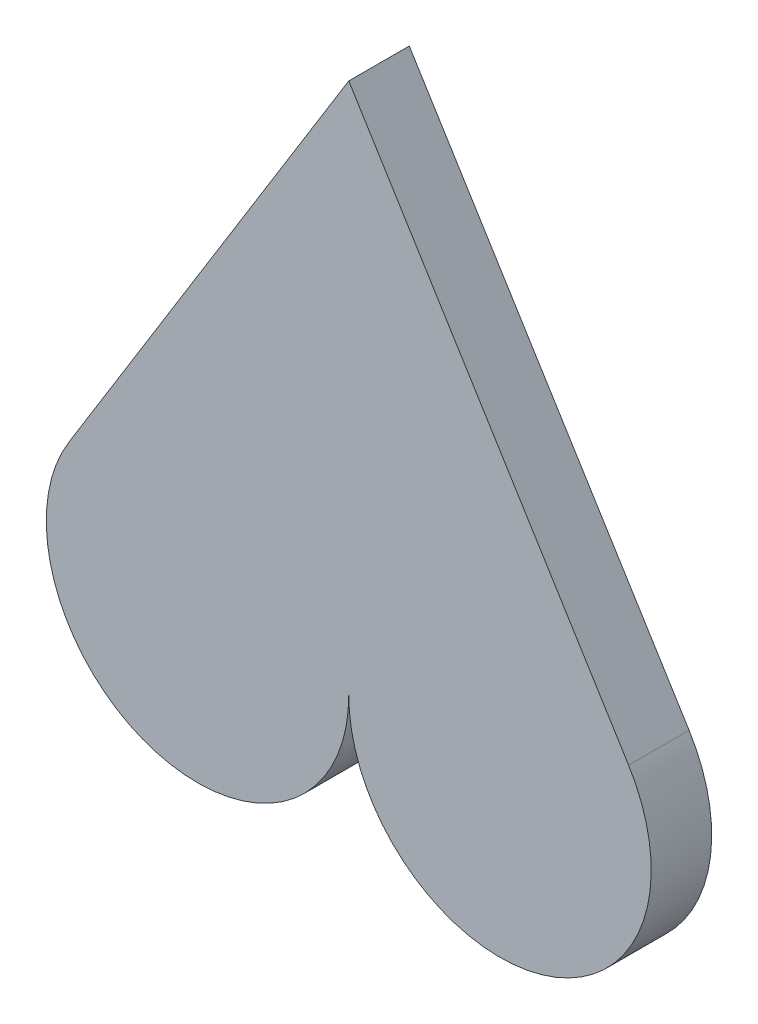
SolidWorks part; units mm, degrees
ref_plane "Front Plane" through (0, 0, 0) normal (0, 0, 1) x (1, 0, 0)
ref_plane "Top Plane" through (0, 0, 0) normal (0, 1, 0) x (1, 0, 0)
ref_plane "Right Plane" through (0, 0, 0) normal (1, 0, 0) x (0, 0, -1)
sketch "Sketch1" plane through (0, 0, 0) normal (0, 0, -1) x (1, 0, 0)
  line L0 (0, 0) -> (-27.7593, 44.9025)
  line L1 (-1000, 0) -> (49000, 0) construction
  line L8 (-0.0012, 0) -> (27.7581, 44.9025)
  arc A0 (-0.0006, 52.7901) -> (-27.7593, 44.9025) centre (-15.0006, 52.7901) ccw
  arc A4 (-0.0006, 52.7901) -> (27.7581, 44.9025) centre (14.9994, 52.7901) cw
  point P2 (-15.0006, 52.7901)
  point P9 (-5.0006, 52.7901)
  point P10 (-23.5064, 47.5317)
  point P11 (4.2529, 2.6292)
  dimension "D1" = 52.7903
extrude "Boss-Extrude1" add sketch "Sketch1" along normal blind 6
